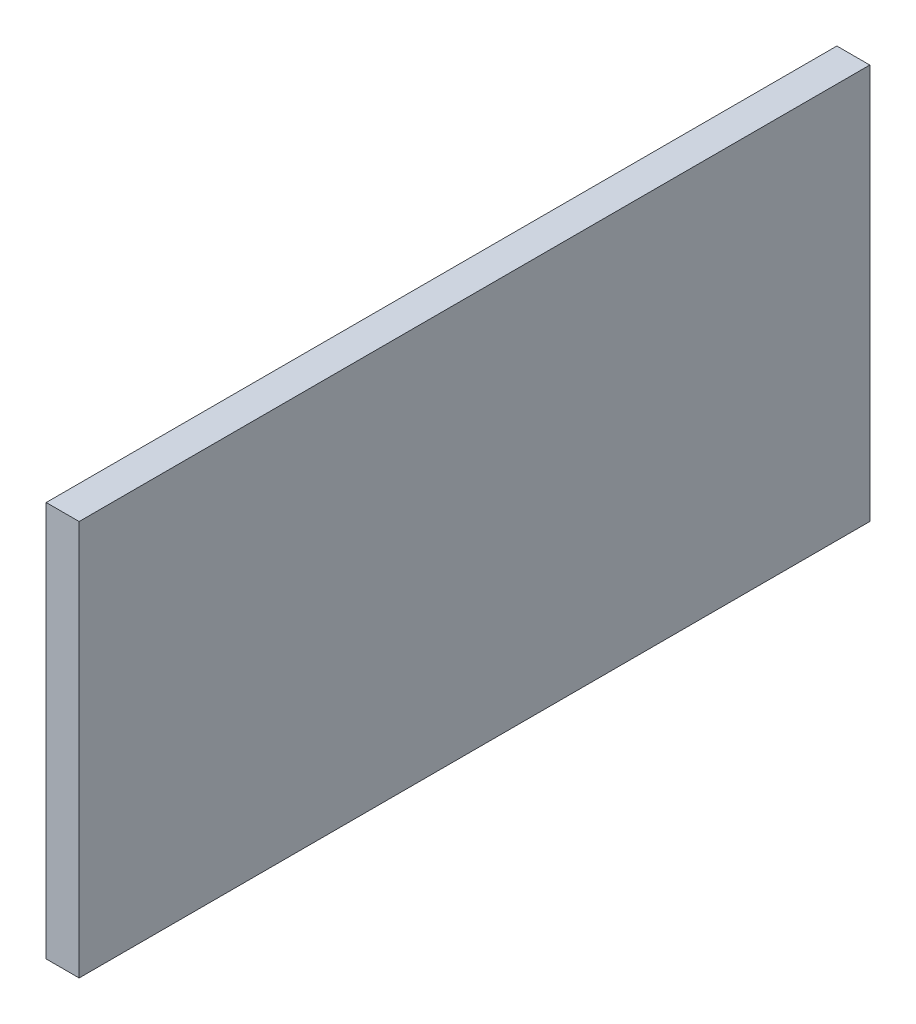
SolidWorks part; units mm, degrees
ref_plane "Front Plane" through (0, 0, 0) normal (0, 0, 1) x (1, 0, 0)
ref_plane "Top Plane" through (0, 0, 0) normal (0, 1, 0) x (1, 0, 0)
ref_plane "Right Plane" through (0, 0, 0) normal (1, 0, 0) x (0, 0, -1)
sketch "Sketch1" plane through (0, 0, 0) normal (1, 0, 0) x (0, 0, -1)
  line L1 (-152.4, 76.2) -> (152.4, 76.2)
  line L2 (-152.4, 76.2) -> (-152.4, -76.2)
  line L3 (-152.4, -76.2) -> (152.4, -76.2)
  line L4 (152.4, 76.2) -> (152.4, -76.2)
  line L5 (-152.4, 76.2) -> (152.4, -76.2) construction
  line L6 (-152.4, -76.2) -> (152.4, 76.2) construction
  point P0 (0, 0)
  dimension "D1" = 304.8
  dimension "D2" = 152.4
extrude "Boss-Extrude1" add sketch "Sketch1" along normal blind 12.7
